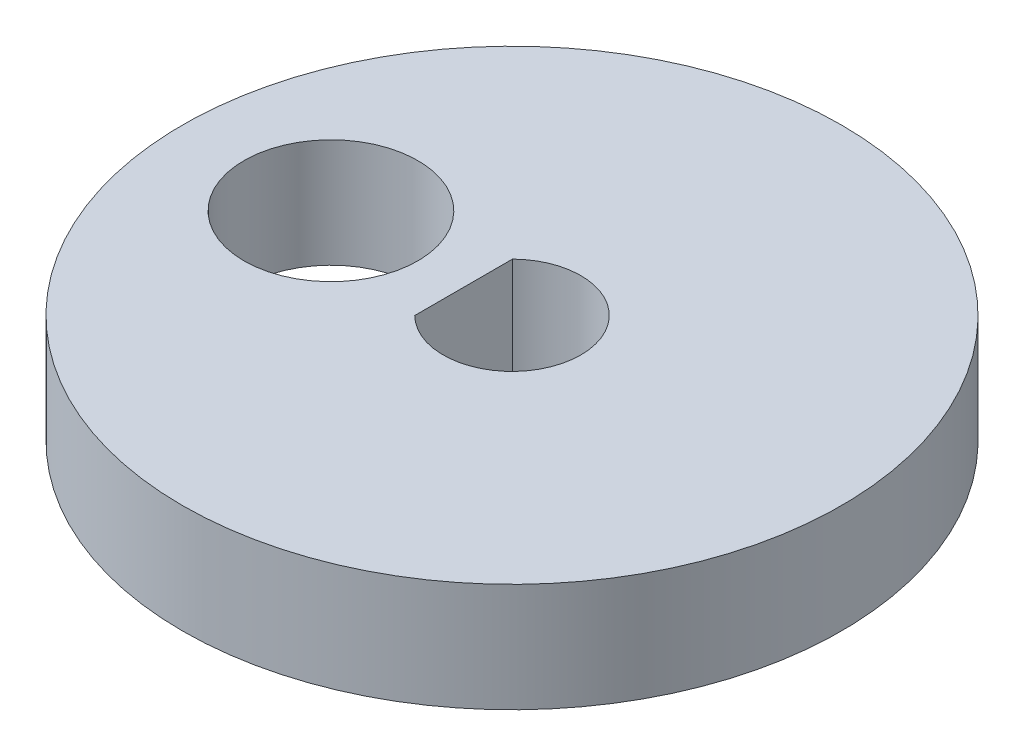
SolidWorks part; units mm, degrees
ref_plane "Front Plane" through (0, 0, 0) normal (0, 0, 1) x (1, 0, 0)
ref_plane "Top Plane" through (0, 0, 0) normal (0, 1, 0) x (1, 0, 0)
ref_plane "Right Plane" through (0, 0, 0) normal (1, 0, 0) x (0, 0, -1)
sketch "Sketch1" plane through (0, 0, 0) normal (0, 1, 0) x (1, 0, 0)
  line L14 (-1.337, 1.35) -> (-1.337, -1.35)
  circle A0 centre (0, 0) radius 9.1
  circle A3 centre (-5, 0) radius 2.4
  arc A4 (-1.337, -1.35) -> (-1.337, 1.35) centre (0, 0) ccw
  dimension "D1" = 18.2
  dimension "D3" = 4.8
  dimension "D15" = 3.8
  dimension "D2" = 5
  dimension "D16" = 2.7
extrude "Boss-Extrude1" add sketch "Sketch1" along normal blind 3
